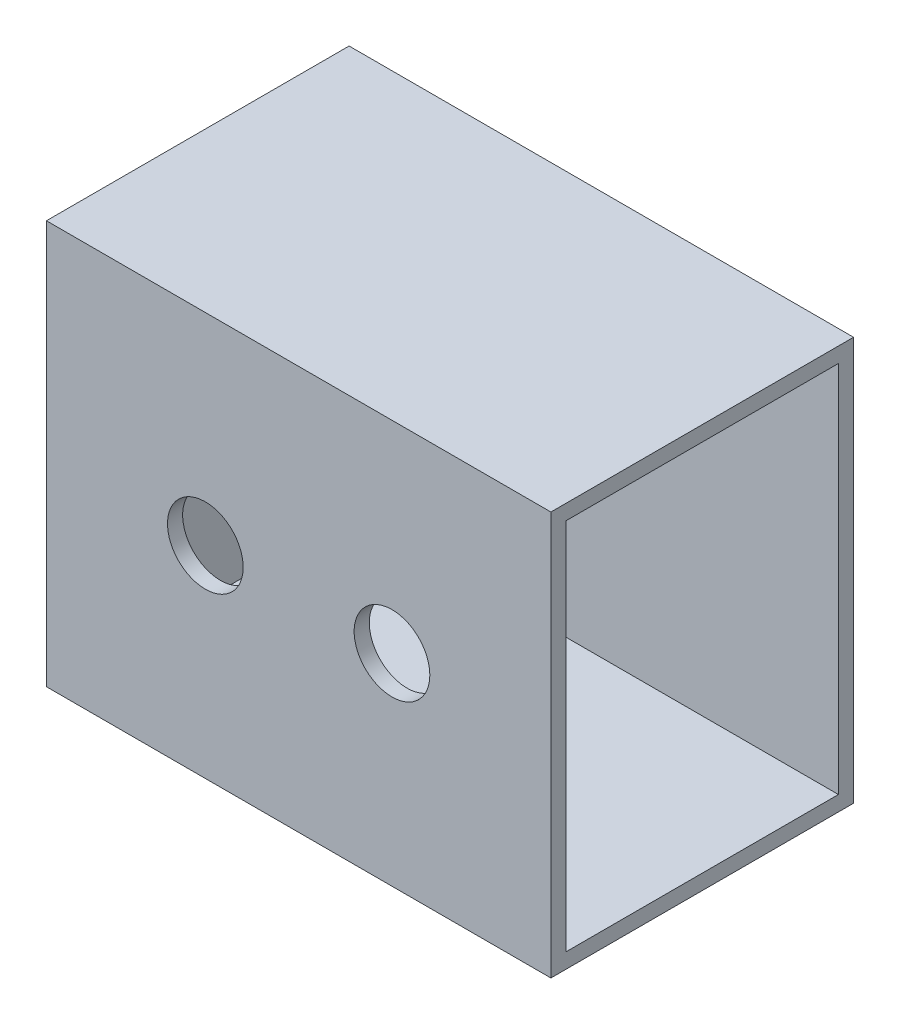
SolidWorks part; units mm, degrees
ref_plane "Front Plane" through (0, 0, 0) normal (0, 0, 1) x (1, 0, 0)
ref_plane "Top Plane" through (0, 0, 0) normal (0, 1, 0) x (1, 0, 0)
ref_plane "Right Plane" through (0, 0, 0) normal (1, 0, 0) x (0, 0, -1)
sketch "Sketch1" plane through (0, 0, 0) normal (0, 0, 1) x (1, 0, 0)
  line L1 (-50, 40) -> (50, 40)
  line L2 (-50, 40) -> (-50, -40)
  line L3 (-50, -40) -> (50, -40)
  line L4 (50, 40) -> (50, -40)
  line L5 (-50, 40) -> (50, -40) construction
  line L6 (-50, -40) -> (50, 40) construction
  line L7 (-46.25, 37) -> (46.25, 37)
  line L8 (-46.25, 37) -> (-46.25, -37)
  line L9 (-46.25, -37) -> (46.25, -37)
  line L10 (46.25, 37) -> (46.25, -37)
  line L11 (-46.25, 37) -> (46.25, -37) construction
  line L12 (-46.25, -37) -> (46.25, 37) construction
  point P0 (0, 0)
  point P6 (0, 0)
  dimension "D1" = 100
  dimension "D2" = 80
  dimension "D3" = 3
extrude "Boss-Extrude1" add sketch "Sketch1" along normal blind 60
sketch "Sketch2" plane through (0, -37, 0) normal (0, 1, 0) x (1, 0, 0)
  line L0 (46.25, -60) -> (46.25, 0) construction
  line L1 (46.25, -3) -> (-46.25, -3)
  line L2 (46.25, -3) -> (46.25, 0)
  line L3 (46.25, 0) -> (-46.25, 0)
  line L4 (-46.25, -3) -> (-46.25, 0)
  dimension "D1" = 3
extrude "Boss-Extrude2" add sketch "Sketch2" along normal blind 77
sketch "Sketch3" plane through (0, -37, 0) normal (0, 1, 0) x (1, 0, 0)
  line L0 (-46.25, -60) -> (-46.25, -3) construction
  line L1 (46.25, -60) -> (-46.25, -60)
  line L2 (46.25, -60) -> (46.25, -57)
  line L3 (46.25, -57) -> (-46.25, -57)
  line L4 (-46.25, -60) -> (-46.25, -57)
  dimension "D1" = 3
extrude "Boss-Extrude3" add sketch "Sketch3" along normal blind 77
sketch "Sketch4" plane through (50, 0, 0) normal (1, 0, 0) x (0, 0, -1)
  line L0 (-60, -40) -> (-60, 40) construction
  line L1 (-57, 37) -> (-3, 37)
  line L2 (-57, 37) -> (-57, -37)
  line L3 (-57, -37) -> (-3, -37)
  line L4 (-3, 37) -> (-3, -37)
  line L5 (-57, 37) -> (-3, -37) construction
  line L6 (-57, -37) -> (-3, 37) construction
  line L7 (0, -40) -> (0, 40) construction
  line L8 (-60, -40) -> (0, -40) construction
  line L9 (-60, 40) -> (0, 40) construction
  point P0 (-30, 0)
  dimension "D1" = 3
  dimension "D2" = 3
  dimension "D3" = 3
  dimension "D4" = 3
extrude "Cut-Extrude1" cut sketch "Sketch4" against normal blind 77
sketch "Sketch7" plane through (0, 0, 60) normal (0, 0, 1) x (1, 0, 0)
  line L0 (50, 0) -> (-50, 0)
  line L1 (50, -40) -> (50, 40) construction
  line L2 (-50, 40) -> (-50, -40) construction
  line L3 (-50, 0) -> (-18.5, 0)
  line L4 (50, 0) -> (18.5, 0)
  circle A0 centre (18.5, 0) radius 7.5
  circle A1 centre (-18.5, 0) radius 7.5
  dimension "D3" = 15
  dimension "D4" = 15
  dimension "D1" = 31.5
  dimension "D2" = 31.5
extrude "Cut-Extrude2" cut sketch "Sketch7" against normal blind 10 contours L4 A0 L0 | L0 A0 L4 | A1
